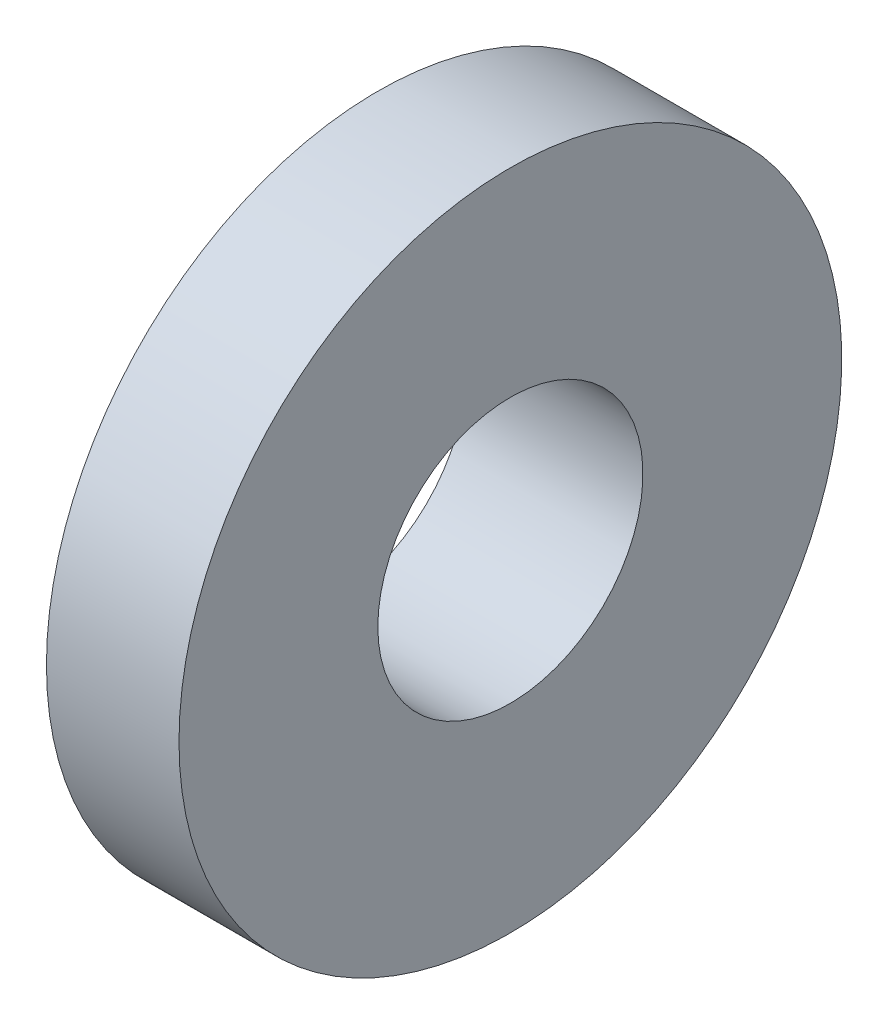
SolidWorks part; units mm, degrees
ref_plane "Front Plane" through (0, 0, 0) normal (0, 0, 1) x (1, 0, 0)
ref_plane "Top Plane" through (0, 0, 0) normal (0, 1, 0) x (1, 0, 0)
ref_plane "Right Plane" through (0, 0, 0) normal (1, 0, 0) x (0, 0, -1)
sketch "Sketch1" plane through (0, 0, 0) normal (0, 0, 1) x (1, 0, 0)
  line L0 (0, 0) -> (8.0937, 0) construction
  line L1 (0, 1.5) -> (0, 2.5)
  line L2 (0, 2.5) -> (0.5, 2.5)
  line L3 (0.5, 2.5) -> (0.5, 3.75)
  line L4 (0.5, 3.75) -> (2, 3.75)
  line L5 (2, 3.75) -> (2, 1.5)
  line L6 (0, 1.5) -> (2, 1.5)
  dimension "D1" = 2
  dimension "D2" = 1.5
  dimension "D3" = 1.5
  dimension "D4" = 3.75
  dimension "D5" = 2.5
revolve "Revolve1" add sketch "Sketch1" angle 360 about L0
scale "Scale1" scale about centroid uniform scaling yes scale factor 1.7
